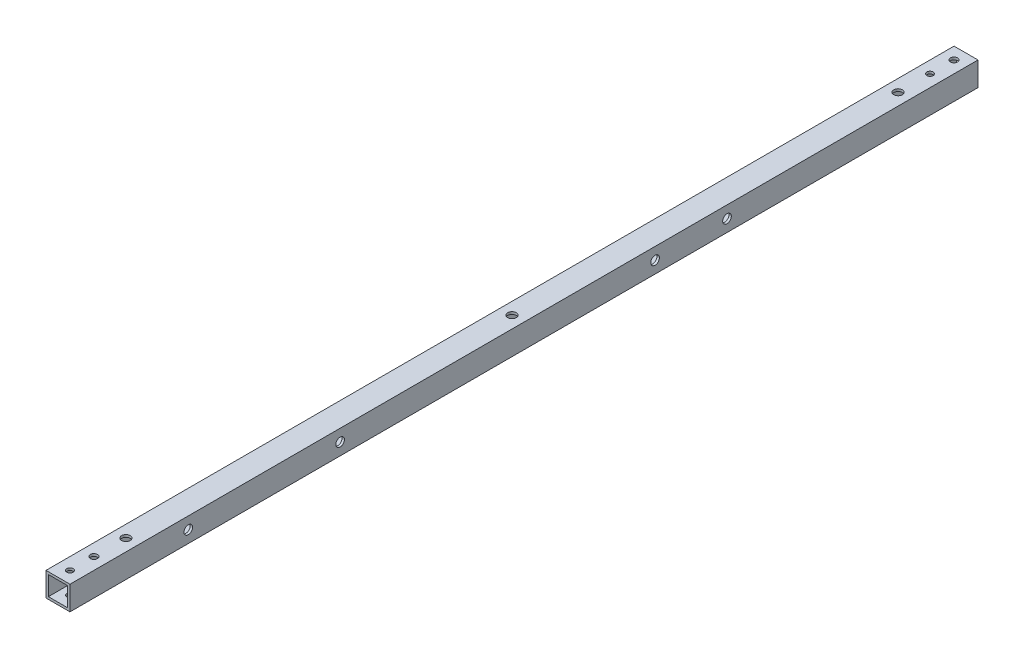
SolidWorks part; units mm, degrees
material "6063-T5"
ref_plane "正面" through (0, 0, 0) normal (0, 0, 1) x (1, 0, 0)
ref_plane "平面" through (0, 0, 0) normal (0, 1, 0) x (1, 0, 0)
ref_plane "右側面" through (0, 0, 0) normal (1, 0, 0) x (0, 0, -1)
sketch "ｽｹｯﾁ1" plane through (0, 0, 0) normal (0, 0, 1) x (1, 0, 0)
  line L1 (-7.5, -7.5) -> (7.5, -7.5)
  line L2 (-7.5, -7.5) -> (-7.5, 7.5)
  line L3 (-7.5, 7.5) -> (7.5, 7.5)
  line L4 (7.5, -7.5) -> (7.5, 7.5)
  line L5 (-7.5, -7.5) -> (7.5, 7.5) construction
  line L6 (-7.5, 7.5) -> (7.5, -7.5) construction
  line L7 (-6, -6) -> (6, -6)
  line L8 (-6, -6) -> (-6, 6)
  line L9 (-6, 6) -> (6, 6)
  line L10 (6, -6) -> (6, 6)
  line L11 (-6, -6) -> (6, 6) construction
  line L12 (-6, 6) -> (6, -6) construction
  point P0 (0, 0)
  point P6 (0, 0)
  dimension "D1" = 1.5
  dimension "D2" = 15
  dimension "D3" = 15
extrude "ﾎﾞｽ - 押し出し1" add sketch "ｽｹｯﾁ1" along normal blind 568
sketch "ｽｹｯﾁ5" plane through (0, -7.5, 0) normal (0, -1, 0) x (-1, 0, 0)
  line L0 (7.5, 0) -> (-7.5, 0) construction
  line L1 (7.5, -568) -> (7.5, 0) construction
  line L2 (7.5, -568) -> (-7.5, -568) construction
  line L3 (-7.5, -568) -> (-7.5, 0) construction
  line L4 (-7.5, -284) -> (7.5, -284) construction
  circle A0 centre (0, -22.5) radius 2
  circle A1 centre (0, -7.5) radius 2.25
  circle A2 centre (0, -560.5) radius 2
  circle A3 centre (0, -545.5) radius 2.25
  circle A4 centre (0, -42.5) radius 2.7
  circle A5 centre (0, -284) radius 2.7
  circle A6 centre (0, -525.5) radius 2.7
  point P20 (-7.5, -284)
  dimension "D1" = 7.5
  dimension "D2" = 4
  dimension "D3" = 4.5
  dimension "D4" = 15
  dimension "D5" = 7.5
  dimension "D6" = 7.5
  dimension "D8" = 7.5
  dimension "D9" = 20
  dimension "D10" = 5.4
  dimension "D7" = 2
extrude "ｶｯﾄ - 押し出し4" cut sketch "ｽｹｯﾁ5" against normal blind 20
sketch "ｽｹｯﾁ9" plane through (7.5, 0, 0) normal (1, 0, 0) x (0, 0, -1)
  line L0 (-568, -7.5) -> (0, -7.5) construction
  line L1 (-568, 7.5) -> (0, 7.5) construction
  circle A0 centre (-494, 0) radius 2.7
  circle A1 centre (-399, 0) radius 2.7
  circle A2 centre (-202, 0) radius 2.7
  circle A3 centre (-157, 0) radius 2.7
  point P12 (-284, 7.5)
  dimension "D1" = 45
  dimension "D2" = 5.4
  dimension "D3" = 5.4
  dimension "D4" = 7.5
  dimension "D5" = 7.5
  dimension "D6" = 82
  dimension "D7" = 115
  dimension "D9" = 5.4
  dimension "D10" = 5.4
  dimension "D12" = 95
  dimension "D8" = 7.5
  dimension "D11" = 7.5
extrude "ｶｯﾄ - 押し出し6" cut sketch "ｽｹｯﾁ9" against normal blind 40
sketch "ｽｹｯﾁ10" plane through (-7.5, 0, 0) normal (-1, 0, 0) x (0, 0, 1)
  circle A0 centre (157, 0) radius 5
  circle A1 centre (202, 0) radius 5
  circle A2 centre (399, 0) radius 5
  circle A4 centre (494, 0) radius 5
  dimension "D1" = 10
  dimension "D2" = 10
  dimension "D3" = 10
  dimension "D4" = 10
extrude "ｶｯﾄ - 押し出し7" cut sketch "ｽｹｯﾁ10" against normal blind 5
hole_wizard "Ø10.0 (10) 直径の穴2" positions "ｽｹｯﾁ13" profile "ｽｹｯﾁ14" hole size "Ø10.0" standard "JIS"
sketch "ｽｹｯﾁ13" plane through (0, -7.5, 0) normal (0, -1, 0) x (-1, 0, 0)
  point P0 (0, -42.5)
  point P3 (0, -284)
  point P6 (0, -525.5)
sketch "ｽｹｯﾁ14" plane through (0, -7.5, 42.5) normal (1, 0, 0) x (0, 0, -1)
  line L0 (0, 0) -> (0, 1.5)
  line L1 (0, 1.5) -> (5, 1.5)
  line L2 (5, 1.5) -> (5, 0)
  line L5 (5, 0) -> (0, 0)
  line L10 (0, 1.5) -> (-5, 1.5) construction
  line L11 (0, -6.35) -> (0, 107.95) construction
  dimension "穴の直径" = 10
  dimension "穴の深さ" = 1.5
  dimension "ﾄﾞﾘﾙ角度" = 180
